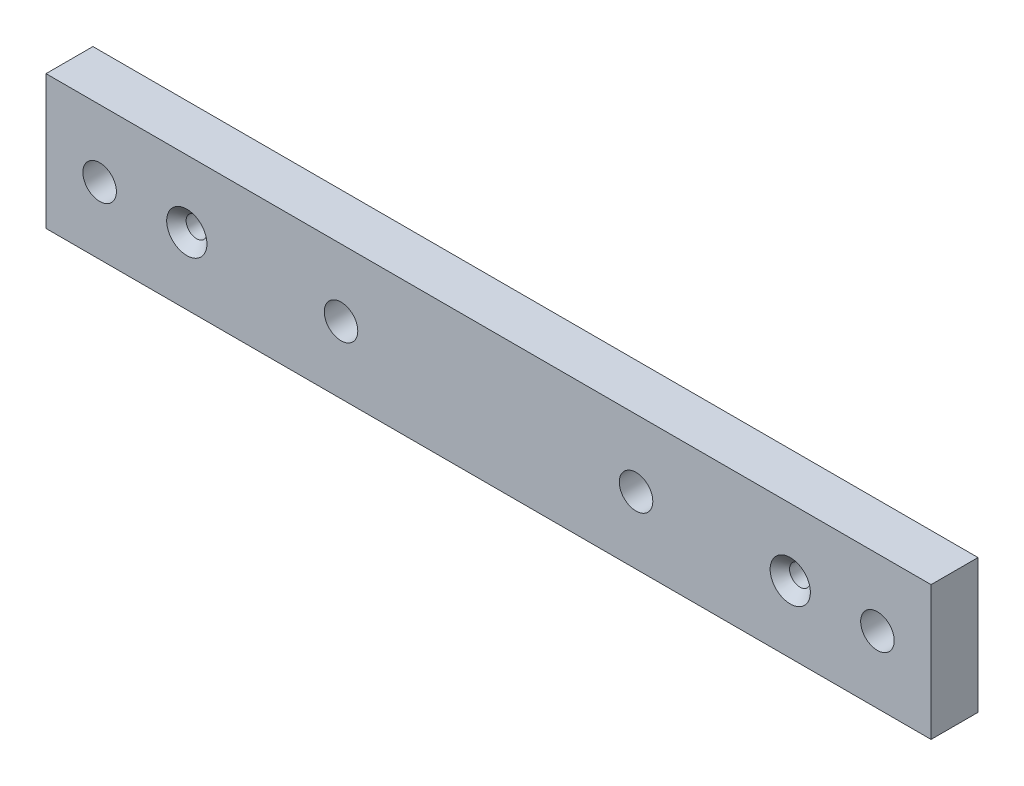
SolidWorks part; units mm, degrees
ref_plane "Front" through (0, 0, 0) normal (0, 0, 1) x (1, 0, 0)
ref_plane "Top" through (0, 0, 0) normal (0, 1, 0) x (1, 0, 0)
ref_plane "Right" through (0, 0, 0) normal (1, 0, 0) x (0, 0, -1)
sketch "Sketch1" plane through (0, 0, 0) normal (0, 0, 1) x (1, 0, 0)
  line L1 (-66, -10) -> (66, -10)
  line L2 (-66, -10) -> (-66, 10)
  line L3 (-66, 10) -> (66, 10)
  line L4 (66, -10) -> (66, 10)
  line L5 (-66, -10) -> (66, 10) construction
  line L6 (-66, 10) -> (66, -10) construction
  circle A0 centre (-45, 0) radius 1.5
  circle A1 centre (45, 0) radius 1.5
  circle A2 centre (-22, 0) radius 2.5
  circle A3 centre (22, 0) radius 2.5
  circle A4 centre (-58, 0) radius 2.5
  circle A5 centre (58, 0) radius 2.5
  point P0 (0, 0)
  dimension "D3" = 3
  dimension "D4" = 3
  dimension "D7" = 5
  dimension "D8" = 5
  dimension "D9" = 22
  dimension "D11" = 5
  dimension "D12" = 5
  dimension "D1" = 20
  dimension "D2" = 132
  dimension "D5" = 90
  dimension "D6" = 45
  dimension "D10" = 22
  dimension "D13" = 13
  dimension "D14" = 13
extrude "Boss-Extrude1" add sketch "Sketch1" along normal blind 7
hole_wizard "CSK for M4 Countersunk Flat Head Screw1" positions "3DSketch1" profile "Sketch2" countersink size "M4" standard "ISO" end condition through all
sketch3d "3DSketch1"
  line L0 (-45, 0, 7) -> (-45, 0, 0) construction
  line L1 (45, 0, 7) -> (45, 0, 0) construction
  point P0 (-45, 0, 7)
  point P4 (45, 0, 7)
sketch "Sketch2" plane through (-45, 0, 7) normal (1, 0, 0) x (0, -1, 0)
  line L0 (0, 0) -> (0, 7)
  line L1 (0, 7) -> (1.55, 7)
  line L2 (1.55, 7) -> (1.55, 1.45)
  line L3 (1.55, 1.45) -> (3, 0)
  line L5 (3, 0) -> (0, 0)
  line L6 (-1.55, 1.45) -> (-3, 0) construction
  line L11 (0, -6.35) -> (0, 107.95) construction
  dimension "Thru Hole Dia." = 3.1
  dimension "Thru Hole Depth" = 7
  dimension "Near C'Sink Dia." = 6
  dimension "Near C'Sink Angle" = 90
